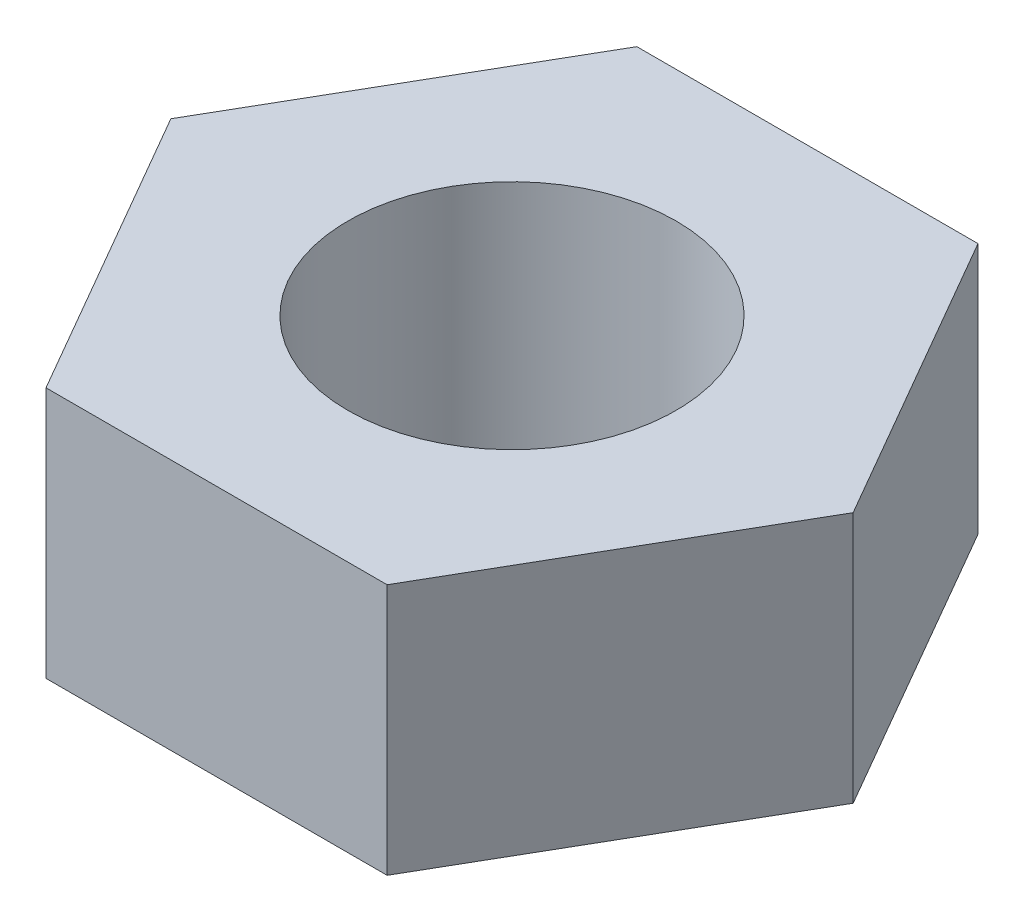
SolidWorks part; units mm, degrees
ref_plane "前视基准面" through (0, 0, 0) normal (0, 0, 1) x (1, 0, 0)
ref_plane "上视基准面" through (0, 0, 0) normal (0, 1, 0) x (1, 0, 0)
ref_plane "右视基准面" through (0, 0, 0) normal (1, 0, 0) x (0, 0, -1)
sketch "草图1" plane through (0, 0, 0) normal (0, 1, 0) x (1, 0, 0)
  line L1 (3.1177, 0) -> (1.5588, 2.7)
  line L2 (1.5588, 2.7) -> (-1.5588, 2.7)
  line L3 (-1.5588, 2.7) -> (-3.1177, 0)
  line L4 (-3.1177, 0) -> (-1.5588, -2.7)
  line L5 (-1.5588, -2.7) -> (1.5588, -2.7)
  line L6 (1.5588, -2.7) -> (3.1177, 0)
  circle A0 centre (0, 0) radius 2.7 construction
  circle A1 centre (0, 0) radius 1.5
extrude "凸台-拉伸1" add sketch "草图1" along normal blind 2.3
